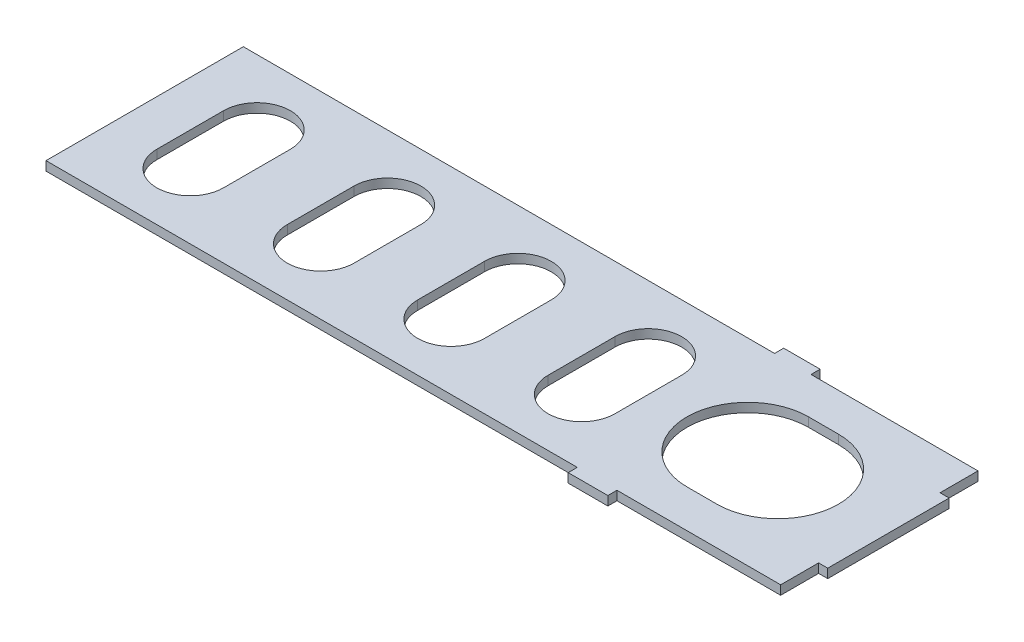
SolidWorks part; units mm, degrees
ref_plane "Front Plane" through (0, 0, 0) normal (0, 0, 1) x (1, 0, 0)
ref_plane "Top Plane" through (0, 0, 0) normal (0, 1, 0) x (1, 0, 0)
ref_plane "Right Plane" through (0, 0, 0) normal (1, 0, 0) x (0, 0, -1)
sketch "Sketch1" plane through (0, 0, 0) normal (0, 1, 0) x (1, 0, 0)
  line L1 (-122.5, -32.5) -> (122.5, -32.5)
  line L2 (-122.5, -32.5) -> (-122.5, 32.5)
  line L3 (-122.5, 32.5) -> (122.5, 32.5)
  line L4 (122.5, -32.5) -> (122.5, 32.5)
  line L5 (-122.5, -32.5) -> (122.5, 32.5) construction
  line L6 (-122.5, 32.5) -> (122.5, -32.5) construction
  point P0 (0, 0)
  dimension "D1" = 65
  dimension "D2" = 245
extrude "Boss-Extrude1" add sketch "Sketch1" along normal blind 3
sketch "Sketch2" plane through (0, 3, 0) normal (0, 1, 0) x (1, 0, 0)
  line L0 (122.5, -32.5) -> (122.5, 32.5) construction
  line L3 (-122.5, -11) -> (122.5, -11) construction
  line L6 (-122.5, -11) -> (-122.5, 11) construction
  line L9 (-122.5, 11) -> (122.5, 11) construction
  line L10 (122.5, -11) -> (122.5, 11) construction
  line L11 (-122.5, -11) -> (122.5, 11) construction
  line L12 (-122.5, 11) -> (122.5, -11) construction
  line L13 (-96.5, 11) -> (-96.5, -11) construction
  line L14 (-85.5, 11) -> (-85.5, -11)
  line L15 (-107.5, 11) -> (-107.5, -11)
  line L22 (86.0358, 0) -> (76.1447, 0) construction
  line L23 (86.0358, -20) -> (76.1447, -20)
  line L24 (86.0358, 20) -> (76.1447, 20)
  line L25 (-64.5301, 11) -> (-64.5301, -11)
  line L28 (-42.5301, 11) -> (-42.5301, -11)
  line L31 (-53.5301, 11) -> (-53.5301, -11) construction
  line L34 (-21.5603, 11) -> (-21.5603, -11)
  line L35 (0.4397, 11) -> (0.4397, -11)
  line L36 (-10.5603, 11) -> (-10.5603, -11) construction
  line L37 (21.4096, 11) -> (21.4096, -11)
  line L38 (43.4096, 11) -> (43.4096, -11)
  line L39 (32.4096, 11) -> (32.4096, -11) construction
  arc A6 (-85.5, 11) -> (-107.5, 11) centre (-96.5, 11) ccw
  arc A7 (-107.5, -11) -> (-85.5, -11) centre (-96.5, -11) ccw
  arc A12 (86.0358, -20) -> (86.0358, 20) centre (86.0358, 0) ccw
  arc A13 (76.1447, 20) -> (76.1447, -20) centre (76.1447, 0) ccw
  arc A22 (-42.5301, 11) -> (-64.5301, 11) centre (-53.5301, 11) ccw
  arc A23 (-64.5301, -11) -> (-42.5301, -11) centre (-53.5301, -11) ccw
  arc A24 (0.4397, 11) -> (-21.5603, 11) centre (-10.5603, 11) ccw
  arc A25 (-21.5603, -11) -> (0.4397, -11) centre (-10.5603, -11) ccw
  arc A26 (43.4096, 11) -> (21.4096, 11) centre (32.4096, 11) ccw
  arc A27 (21.4096, -11) -> (43.4096, -11) centre (32.4096, -11) ccw
  point P0 (0, 0)
  point P10 (-96.5, 0)
  point P19 (-53.5301, 0)
  point P26 (-10.5603, 0)
  point P31 (81.0903, 0)
  point P40 (32.4096, 0)
  dimension "D1" = 22
  dimension "D2" = 20
  dimension "D3" = 4
  dimension "D4" = 11
  dimension "D5" = 26
extrude "Cut-Extrude1" cut sketch "Sketch2" against normal blind 10
sketch "Sketch3" plane through (0, 3, 0) normal (0, 1, 0) x (1, 0, 0)
  line L0 (122.5, 32.5) -> (-122.5, 32.5) construction
  line L1 (119.5, 32.5) -> (122.5, 32.5)
  line L2 (119.5, 32.5) -> (119.5, 20)
  line L3 (119.5, 20) -> (122.5, 20)
  line L4 (122.5, 32.5) -> (122.5, 20)
  line L5 (122.5, -32.5) -> (122.5, 32.5) construction
  line L6 (-122.5, -32.5) -> (122.5, -32.5) construction
  line L7 (122.5, -20) -> (119.5, -20)
  line L8 (122.5, -20) -> (122.5, -32.5)
  line L9 (122.5, -32.5) -> (119.5, -32.5)
  line L10 (119.5, -20) -> (119.5, -32.5)
  dimension "D1" = 3
  dimension "D2" = 40
extrude "Cut-Extrude2" cut sketch "Sketch3" against normal blind 10
sketch "Sketch5" plane through (0, 3, 0) normal (0, 1, 0) x (1, 0, 0)
  line L0 (119.5, 32.5) -> (-122.5, 32.5) construction
  line L1 (52.5, 32.5) -> (64.5, 32.5)
  line L2 (52.5, 32.5) -> (52.5, 35.5)
  line L3 (52.5, 35.5) -> (64.5, 35.5)
  line L4 (64.5, 32.5) -> (64.5, 35.5)
  line L5 (-122.5, -32.5) -> (119.5, -32.5) construction
  line L6 (52.5, -32.5) -> (65.5714, -32.5)
  line L7 (52.5, -32.5) -> (52.5, -35.5)
  line L8 (52.5, -35.5) -> (65.5714, -35.5)
  line L9 (65.5714, -32.5) -> (65.5714, -35.5)
  line L10 (122.5, -20) -> (122.5, 20) construction
  dimension "D1" = 12
  dimension "D2" = 3
  dimension "D3" = 70
extrude "Boss-Extrude2" add sketch "Sketch5" against normal up to surface (3 mm away) up to face at (59.75, 0, 0)
